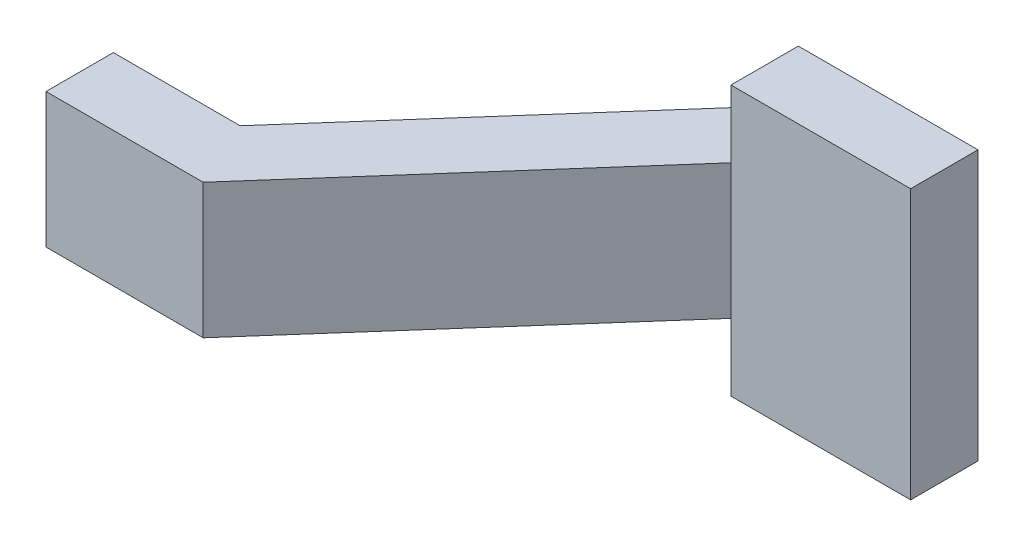
SolidWorks part; units mm, degrees
ref_plane "Front Plane" through (0, 0, 0) normal (0, 0, 1) x (1, 0, 0)
ref_plane "Top Plane" through (0, 0, 0) normal (0, 1, 0) x (1, 0, 0)
ref_plane "Right Plane" through (0, 0, 0) normal (1, 0, 0) x (0, 0, -1)
sketch "Sketch1" plane through (0, 0, 0) normal (0, 1, 0) x (1, 0, 0)
  line L0 (0, 0) -> (0.889, 0)
  line L1 (0.889, 0) -> (2.286, 1.5875)
  line L2 (2.286, 1.5875) -> (3.302, 1.5875)
  line L3 (3.302, 1.5875) -> (3.302, 1.9685)
  line L4 (0, 0) -> (0, 0.381)
  line L5 (0.7168, 0.381) -> (2.1138, 1.9685)
  line L6 (1.6109, 0.8204) -> (1.3249, 1.0721) construction
  line L7 (0, 0.381) -> (0.7168, 0.381)
  line L8 (3.302, 1.9685) -> (2.1138, 1.9685)
  dimension "D1" = 3.302
  dimension "D2" = 0.381
  dimension "D3" = 0.889
  dimension "D4" = 1.016
  dimension "D5" = 1.9685
extrude "Boss-Extrude1" add sketch "Sketch1" along normal mid plane 1.524
sketch "Sketch2" plane through (0, 0, -1.9685) normal (0, 0, -1) x (-1, 0, 0)
  line L0 (-2.286, 0.762) -> (-2.286, -0.762) construction
  line L1 (0, 0.762) -> (-2.286, 0.762)
  line L2 (0, 0.762) -> (0, 0.381)
  line L3 (0, 0.381) -> (-2.286, 0.381)
  line L4 (-2.286, 0.762) -> (-2.286, 0.381)
  line L6 (0.8071, 0) -> (-0.8071, 0) construction
  dimension "D1" = 0.381
extrude "Cut-Extrude1" cut sketch "Sketch2" against normal through all
mirror "Mirror1" about plane through (0, 0, 0) normal (0, 1, 0) of "Cut-Extrude1"
ref_plane "Plane1" through (0, 0, -1.778) normal (0, 0, -1) x (-1, 0, 0)
